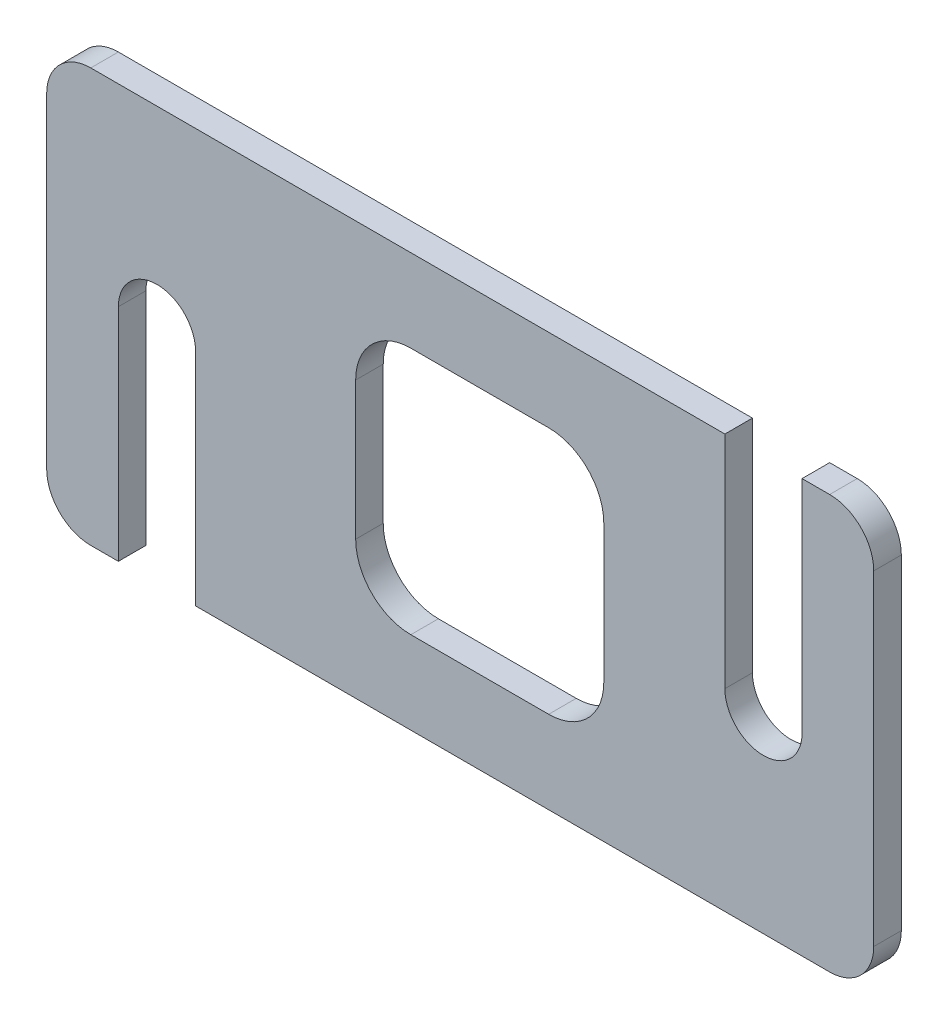
SolidWorks part; units mm, degrees
ref_plane "Front Plane" through (0, 0, 0) normal (0, 0, 1) x (1, 0, 0)
ref_plane "Top Plane" through (0, 0, 0) normal (0, 1, 0) x (1, 0, 0)
ref_plane "Right Plane" through (0, 0, 0) normal (1, 0, 0) x (0, 0, -1)
sketch "Sketch1" plane through (0, 0, 0) normal (0, 0, 1) x (1, 0, 0)
  line L0 (0, 0) -> (150, 0)
  line L1 (150, 0) -> (150, 75)
  line L2 (150, 75) -> (0, 75)
  line L3 (0, 75) -> (0, 0)
  dimension "D1" = 150
  dimension "D2" = 75
extrude "Boss-Extrude2" add sketch "Sketch1" along normal blind 5
sketch "Sketch2" plane through (0, 0, 0) normal (0, 0, 1) x (1, 0, 0)
  line L0 (56.0399, 50) -> (56.0399, 25)
  line L1 (101.0399, 25) -> (101.0399, 50)
  line L2 (91.0399, 60) -> (66.0399, 60)
  line L3 (66.0399, 15) -> (91.0399, 15)
  line L4 (0, 0) -> (150, 0) construction
  line L5 (150, 75) -> (0, 75) construction
  line L6 (20, 0) -> (20, 40) construction
  line L7 (13, 0) -> (13, 40)
  line L8 (27, 0) -> (27, 40)
  arc A0 (13, 0) -> (27, 0) centre (20, 0) ccw
  arc A1 (27, 40) -> (13, 40) centre (20, 40) ccw
  arc A2 (56.0399, 25) -> (66.0399, 15) centre (66.0399, 25) ccw
  arc A3 (101.0399, 25) -> (91.0399, 15) centre (91.0399, 25) cw
  arc A4 (101.0399, 50) -> (91.0399, 60) centre (91.0399, 50) ccw
  arc A5 (56.0399, 50) -> (66.0399, 60) centre (66.0399, 50) cw
  point P10 (20, 20)
  point P21 (101.0399, 60)
  point P24 (56.0399, 60)
  dimension "D4" = 10
  dimension "D6" = 7
  dimension "D1" = 15
  dimension "D2" = 15
  dimension "D3" = 45
  dimension "D5" = 20
  dimension "D7" = 40
extrude "Cut-Extrude9" cut sketch "Sketch2" along normal through all and the other way through all contours L3 A3 L1 A4 L2 A5 L0 A2 | L8 A1 L7 A0
sketch "Sketch3" plane through (0, 0, 5) normal (0, 0, 1) x (1, 0, 0)
  line L0 (137, 35) -> (137, 75)
  line L1 (150, 75) -> (0, 75) construction
  line L2 (123, 75) -> (123, 35)
  arc A0 (123, 35) -> (137, 35) centre (130, 35) ccw
  dimension "D1" = 7
  dimension "D2" = 40
  dimension "D3" = 13
extrude "Cut-Extrude10" cut sketch "Sketch3" against normal through all and the other way through all
fillet "Fillet3" radius 8 1 edges at (150, 75, 2.5)
fillet "Fillet4" radius 8 1 edges at (0, 0, 2.5)
fillet "Fillet5" radius 8 1 edges at (150, 0, 2.5)
fillet "Fillet6" radius 8 1 edges at (0, 75, 2.5)
